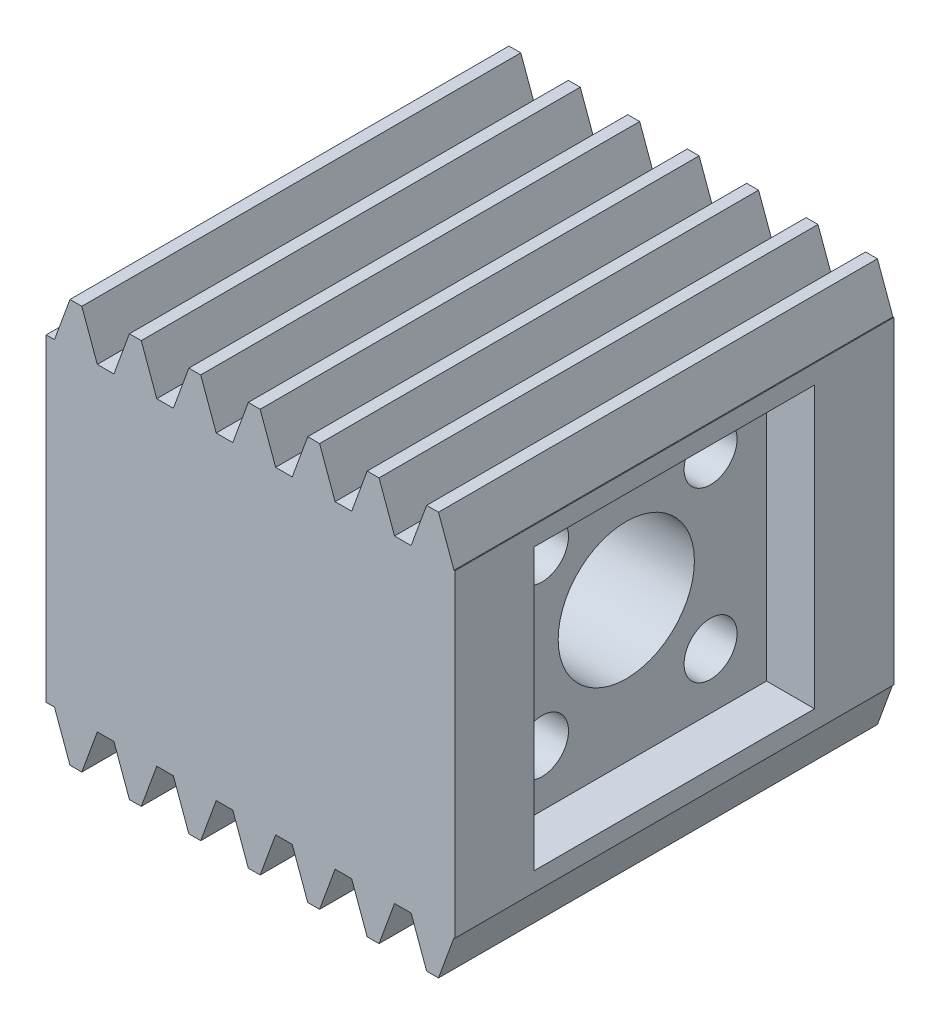
SolidWorks part; units mm, degrees
extrude "Blank" add sketch "BlankSke" against normal blind 29
sketch "BlankSke" plane through (0, 0, 0) normal (0, 0, 1) x (1, 0, 0)
  line L1 (0, 0) -> (27, 0)
  line L2 (0, 0) -> (0, 13.325)
  line L3 (0, 13.325) -> (27, 13.325)
  line L4 (27, 0) -> (27, 13.325)
  dimension "Length" = 27
  dimension "Blank_height" = 13.325
ref_plane "Plane1" through (0, 0, 0) normal (0, 0, 1) x (1, 0, 0)
ref_plane "Plane2" through (0, 0, 0) normal (0, 1, 0) x (1, 0, 0)
ref_plane "Plane3" through (0, 0, 0) normal (1, 0, 0) x (0, 0, -1)
sketch "HoldingSke" plane through (0, 0, 0) normal (0, 1, 0) x (1, 0, 0)
  line L0 (0, 0) -> (0.1113, 0.7922)
  line L1 (-15, 0) -> (100, 0) construction
  line L2 (0, 0) -> (-2.1039, 2.3779)
  line L3 (0, 0) -> (-11.863, 4.5341)
  line L4 (0, 0) -> (8.552, 1.2019)
  line L5 (0, 0) -> (-23.7986, -8.8762)
  line L6 (0, 0) -> (-10.5278, -7.1032)
  line L9 (-71.009, 38.7566) -> (-45.6373, 47.9912)
  line L10 (-76.2, 3.6279) -> (-64.125, 3.6279)
  line L11 (0, 0) -> (-29, 0)
  line L12 (-76.2, 101.6) -> (-76.155, 101.6)
  line L13 (24.9733, 27.94) -> (52.9518, 28.4284)
  line L14 (24.9733, 27.94) -> (24.9743, 27.94)
  line L15 (24.9733, 27.94) -> (100.4006, 29.5858)
  circle A0 centre (0, 0) radius 19.05
  circle A1 centre (0, 0) radius 6.0375
  circle A2 centre (0, 0) radius 12.7
  dimension "MPH" = 12.075
  dimension "Diameter" = 38.1
  dimension "Num_teeth" = 8
  dimension "Pitch" = 0.8
  dimension "Show_teeth" = 998
  dimension "Thickness" = 12.7
  dimension "Ap" = 20
  dimension "Pitch_height" = 12.075
  dimension "Width" = 29
  dimension "Backlash" = 0.045
  dimension "Addendum_fac" = 1
  dimension "Dedendum_fac" = 1.25
  dimension "Clearance_fac" = 0.25
  dimension "Dedendum_add" = 0.001
  dimension "Length" = 27
  dimension "Module" = 1.25
sketch "TooCutSkeIll" plane through (0, 0, 0) normal (0, 0, 1) x (1, 0, 0)
  line L0 (-1.5597, 13.2921) -> (-0.6231, 10.7188)
  line L1 (-0.3285, 10.5125) -> (0.3285, 10.5125)
  line L2 (0.6231, 10.7188) -> (1.5597, 13.2921)
  line L3 (27, 13.325) -> (0, 13.325) construction
  line L4 (0, 0) -> (0, 64.897) construction
  line L5 (-13.208, 12.075) -> (12.954, 12.075) construction
  line L6 (0, 0) -> (27, 0) construction
  line L7 (1.1167, 12.075) -> (1.1167, 48.7463) construction
  line L8 (-1.1167, 12.075) -> (-1.1167, 48.7463) construction
  line L9 (1.6067, 13.325) -> (1.6067, 13.3504)
  line L10 (-1.6067, 13.325) -> (-1.6067, 13.3504)
  line L11 (-1.6067, 13.3504) -> (1.6067, 13.3504)
  arc A0 (0.3285, 10.5125) -> (0.6231, 10.7188) centre (0.3285, 10.826) ccw
  arc A1 (-0.6231, 10.7188) -> (-0.3285, 10.5125) centre (-0.3285, 10.826) ccw
  arc A2 (1.6067, 13.325) -> (1.5597, 13.2921) centre (1.6067, 13.275) ccw
  arc A3 (-1.5597, 13.2921) -> (-1.6067, 13.325) centre (-1.6067, 13.275) ccw
  dimension "Pitch_height" = 12.075
  dimension "Addendum_plus" = 1.2754
  dimension "Pressure_angle" = 20
  dimension "Gap_width" = 2.2335
  dimension "Dedendum" = 1.5625
extrude "ToothCutIll" [suppressed] cut sketch "TooCutSkeIll" against normal through all
sketch "TooCutSkeSim" plane through (0, 0, 0) normal (0, 0, 1) x (1, 0, 0)
  line L0 (0.548, 10.5125) -> (-0.548, 10.5125)
  line L1 (1.581, 13.3504) -> (0.548, 10.5125)
  line L2 (0, 17.4625) -> (0, 53.467) construction
  line L3 (1.581, 13.3504) -> (-1.581, 13.3504)
  line L6 (-1.581, 13.3504) -> (-0.548, 10.5125)
  line L9 (-1.1167, 12.075) -> (1.1167, 12.075) construction
  line L10 (0, 0) -> (27, 0) construction
  line L11 (1.1167, 12.075) -> (1.1167, 53.467) construction
  line L12 (-1.1167, 12.075) -> (-1.1167, 53.467) construction
  dimension "Pitch_height" = 12.075
  dimension "Addendum_plus" = 1.2754
  dimension "Pressure_angle" = 20
  dimension "Gap_width" = 2.2335
  dimension "Dedendum" = 1.5625
extrude "ToothCutSim" cut sketch "TooCutSkeSim" against normal through all
pattern_linear "TeethCuts" count 8 spacing 3.927 along (1, 0, 0) of "ToothCutIll", "ToothCutSim"
sketch "Sketch2" plane through (0, 0, 0) normal (-1, 0, 0) x (0, 0, 1)
  line L0 (-29, 0) -> (0, 0) construction
  line L1 (-7.445, 8.763) -> (-21.555, 8.763)
  line L4 (-3.25, 0) -> (-25.75, 0)
  arc A0 (-21.555, 8.763) -> (-25.75, 0) centre (-14.5, 0) ccw
  arc A1 (-3.25, 0) -> (-7.445, 8.763) centre (-14.5, 0) ccw
  dimension "D1" = 8.763
  dimension "D2" = 22.5
extrude "Cut-Extrude1" cut sketch "Sketch2" against normal blind 6.75
sketch "Sketch3" plane through (6.75, 0, 0) normal (-1, 0, 0) x (0, 0, 1)
  line L0 (-3.25, 0) -> (-25.75, 0) construction
  circle A0 centre (-14.5, 0) radius 5.25
extrude "Cut-Extrude2" cut sketch "Sketch3" against normal blind 10.25
sketch "Sketch4" plane through (17, 0, 0) normal (-1, 0, 0) x (0, 0, 1)
  line L0 (-9.25, 0) -> (-19.75, 0) construction
  circle A0 centre (-14.5, 0) radius 4.5
extrude "Cut-Extrude3" cut sketch "Sketch4" against normal through all both and the other way through all
sketch "Sketch5" plane through (27, 0, 0) normal (1, 0, 0) x (0, 0, -1)
  circle A0 centre (14.5, 0) radius 7.874 construction
  circle A1 centre (8.9322, 5.5678) radius 2.5
  circle A2 centre (20.0678, 5.5678) radius 2.5
extrude "Cut-Extrude4" cut sketch "Sketch5" against normal blind 3.175
sketch "Sketch6" plane through (23.825, 0, 0) normal (1, 0, 0) x (0, 0, -1)
  circle A0 centre (20.0678, 5.5678) radius 1.75
  circle A1 centre (8.9322, 5.5678) radius 1.75
extrude "Cut-Extrude5" cut sketch "Sketch6" against normal through all
mirror "Mirror1" about plane through (0, 0, -29) normal (0, -1, 0) of "Cut-Extrude2", "Cut-Extrude3", "Cut-Extrude1", "TeethCuts", "ToothCutSim", "Blank", "Cut-Extrude5", "Cut-Extrude4"
ref_plane "Plane4" through (0, 0, -14.5) normal (0, 0, 1) x (1, 0, 0)
sketch "Sketch7" plane through (0, 0, -14.5) normal (0, 0, 1) x (1, 0, 0)
  line L0 (0, 10.5125) -> (0, -10.5125) construction
  line L2 (0, -12.075) -> (27.3762, -12.075)
  point P3 (0, 0)
  dimension "D1" = 12.075
sketch "Sketch8" plane through (0, 0, -14.5) normal (0, 0, 1) x (1, 0, 0)
  line L0 (27.2819, 12.075) -> (0, 12.075)
  line L2 (0, 10.5125) -> (0, -10.5125) construction
  point P6 (0, 0)
  dimension "D1" = 12.075
sketch "Sketch9" plane through (27, 0, 0) normal (1, 0, 0) x (0, 0, -1)
  line L0 (7.445, 8.763) -> (21.555, 8.763) construction
  line L1 (5.737, -8.763) -> (23.263, -8.763)
  line L2 (5.737, -8.763) -> (5.737, 8.763)
  line L3 (5.737, 8.763) -> (23.263, 8.763)
  line L4 (23.263, -8.763) -> (23.263, 8.763)
  line L5 (5.737, -8.763) -> (23.263, 8.763) construction
  line L6 (5.737, 8.763) -> (23.263, -8.763) construction
  line L7 (7.445, 8.763) -> (21.555, 8.763)
  line L8 (23.763, -9.263) -> (23.763, 9.263)
  line L9 (5.237, 9.263) -> (23.763, 9.263)
  line L10 (5.237, -9.263) -> (5.237, 9.263)
  line L11 (5.237, -9.263) -> (23.763, -9.263)
  circle A0 centre (20.0678, 5.5678) radius 1.25
  circle A1 centre (20.0678, -5.5678) radius 1.25
  circle A2 centre (8.9322, 5.5678) radius 1.25
  circle A3 centre (8.9322, -5.5678) radius 1.25
  point P12 (14.5, 0)
  dimension "D1" = 2.5
  dimension "D2" = 3.1952
  dimension "D3" = 3.1952
extrude "Cut-Extrude6" cut sketch "Sketch9" against normal blind 3.175 contours L8 L9 L10 L11
equation "' \"Module@HoldingSke\" = 6.35"
equation "' \"Num_teeth@HoldingSke\" = 12"
equation "' \"Ap@HoldingSke\" =  20"
equation "' \"Ap@HoldingSke\" = 20"
equation "' \"Width@HoldingSke\" = 0.25 * 25.4"
equation "' \"Show_teeth@HoldingSke\" = 500"
equation "' \"Backlash@HoldingSke\" = 0.009 * 25.4"
equation "' \"Addendum_fac@HoldingSke\" = 1.0"
equation "' \"Dedendum_fac@HoldingSke\" = 1.25"
equation "' \"Dedendum_add@HoldingSke\" = 0.00005 * 25.4"
equation "' \"Clearance_fac@HoldingSke\" = 0.25"
equation "' \"Pitch_height@HoldingSke\" = 1 * 25.4"
equation "' \"Length@HoldingSke\" = 4.71 * 25.4"
equation "\"Pitch@HoldingSke\" = 1 / \"Module@HoldingSke\""
equation "\"MPH@HoldingSke\" = \"Dedendum_fac@HoldingSke\" / \"Pitch@HoldingSke\" + 2 * \"Dedendum_add@HoldingSke\" + 0.002 * 25.4"
equation "\"MPH@HoldingSke\" = ((sgn( \"MPH@HoldingSke\" - \"Pitch_height@HoldingSke\")+1)*( \"MPH@HoldingSke\" - \"Pitch_height@HoldingSke\"))/2 + \"Pitch_height@HoldingSke\""
equation "\"Blank_height@BlankSke\" = \"Pitch_height@HoldingSke\" + \"Addendum_fac@HoldingSke\"  / \"Pitch@HoldingSke\" "
equation "\"Length@BlankSke\" =  \"Length@HoldingSke\""
equation "\"Face_width@Blank\" = \"Width@HoldingSke\""
equation "\"Pressure_angle@TooCutSkeIll\" = \"Ap@HoldingSke\""
equation "\"Addendum_plus@TooCutSkeIll\" =  \"Addendum_fac@HoldingSke\"  / \"Pitch@HoldingSke\" + 0.001 *25.4"
equation "\"Dedendum@TooCutSkeIll\" = \"Dedendum_fac@HoldingSke\"  / \"Pitch@HoldingSke\""
equation "\"Pitch_height@TooCutSkeIll\" =  \"MPH@HoldingSke\""
equation "\"Gap_width@TooCutSkeIll\" = 3.14159265 / 2 / \"Pitch@HoldingSke\" + 6 * \"Backlash@HoldingSke\""
equation "\"Pressure_angle@TooCutSkeSim\" = \"Ap@HoldingSke\""
equation "\"Addendum_plus@TooCutSkeSim\" =  \"Addendum_fac@HoldingSke\"  / \"Pitch@HoldingSke\" + 0.001 * 25.4"
equation "\"Dedendum@TooCutSkeSim\" = \"Dedendum_fac@HoldingSke\"  / \"Pitch@HoldingSke\""
equation "\"Pitch_height@TooCutSkeSim\" =  \"MPH@HoldingSke\""
equation "\"Gap_width@TooCutSkeSim\" = 3.14159265 / 2 / \"Pitch@HoldingSke\" + 6 * \"Backlash@HoldingSke\""
equation "\"Root_fillet@TooCutSkeIll\" = \"Clearance_fac@HoldingSke\" / \"Pitch@HoldingSke\" + \"Dedendum_add@HoldingSke\""
equation "\"Break_rad@TooCutSkeIll\" = 0.02 / \"Pitch@HoldingSke\" * 2"
equation "\"Linear_pitch@TeethCuts\" = 3.14159265 / \"Pitch@HoldingSke\""
equation "\"Num_teeth@HoldingSke\" = int( ( \"Length@HoldingSke\" + 0 ) / (3.14159265 / \"Pitch@HoldingSke\")) + 0.9999  + 1"
equation " \"Num_teeth@TeethCuts\" = int( \"Show_teeth@HoldingSke\" ) + 1"
equation " \"Num_teeth@TeethCuts\" = ((sgn( \"Num_teeth@TeethCuts\" - \"Num_teeth@HoldingSke\" )-1)*( \"Num_teeth@TeethCuts\" - \"Num_teeth@HoldingSke\" ))/-2+ \"Num_teeth@HoldingSke\""
equation " \"Num_teeth@TeethCuts\" = ((sgn( \"Num_teeth@TeethCuts\" - 2.0)+1)*( \"Num_teeth@TeethCuts\" - 2.0))/2 +2.0"
equation "\"D3@Sketch9\"=\"D2@Sketch9\""
